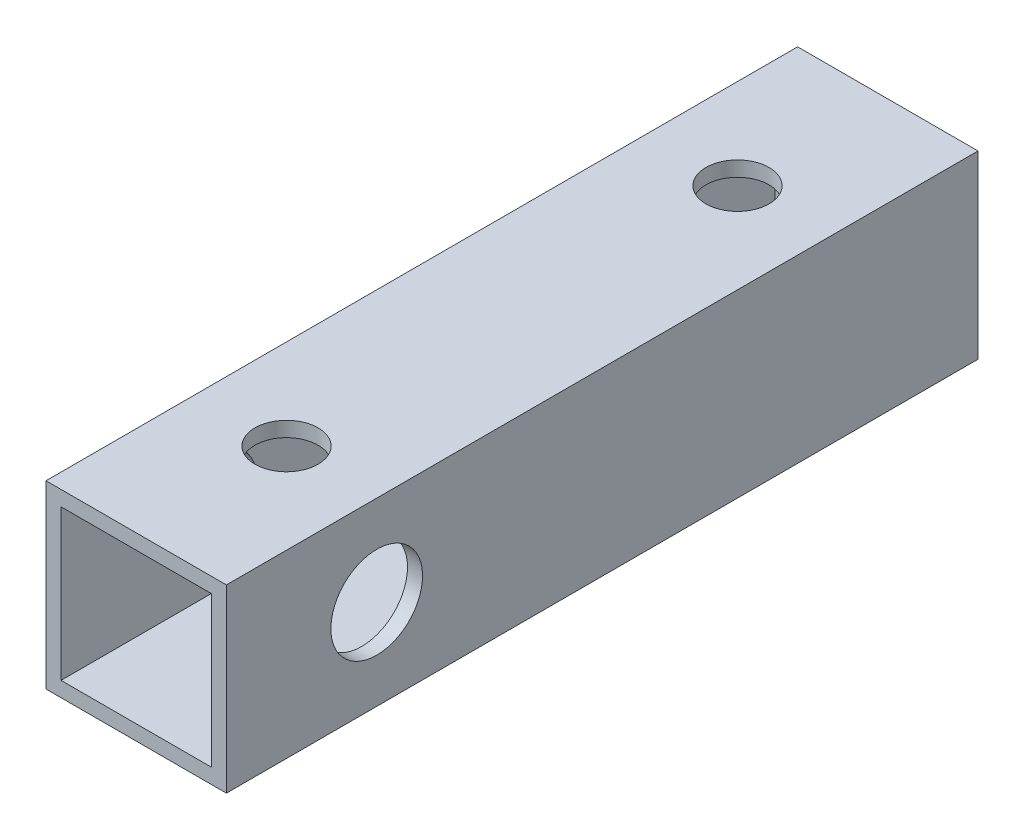
SolidWorks part; units mm, degrees
ref_plane "正面" through (0, 0, 0) normal (0, 0, 1) x (1, 0, 0)
ref_plane "平面" through (0, 0, 0) normal (0, 1, 0) x (1, 0, 0)
ref_plane "右側面" through (0, 0, 0) normal (1, 0, 0) x (0, 0, -1)
sketch "ｽｹｯﾁ1" plane through (0, 0, 0) normal (0, 0, 1) x (1, 0, 0)
  line L1 (-6, 6) -> (6, 6)
  line L2 (-6, 6) -> (-6, -6)
  line L3 (-6, -6) -> (6, -6)
  line L4 (6, 6) -> (6, -6)
  line L5 (-6, 6) -> (6, -6) construction
  line L6 (-6, -6) -> (6, 6) construction
  point P0 (0, 0)
  dimension "D1" = 12
  dimension "D2" = 12
extrude "ﾎﾞｽ - 押し出し1" add sketch "ｽｹｯﾁ1" along normal blind 50
sketch "ｽｹｯﾁ2" plane through (0, 0, 50) normal (0, 0, 1) x (1, 0, 0)
  line L1 (-5, 5) -> (5, 5)
  line L2 (-5, 5) -> (-5, -5)
  line L3 (-5, -5) -> (5, -5)
  line L4 (5, 5) -> (5, -5)
  line L5 (-5, 5) -> (5, -5) construction
  line L6 (-5, -5) -> (5, 5) construction
  point P0 (0, 0)
  dimension "D1" = 10
  dimension "D2" = 10
extrude "ｶｯﾄ - 押し出し1" cut sketch "ｽｹｯﾁ2" against normal blind 47.5
sketch "ｽｹｯﾁ3" plane through (0, 6, 0) normal (0, 1, 0) x (1, 0, 0)
  line L0 (0, 0) -> (0, -10)
  line L1 (0, -50) -> (0, -40)
  line L2 (6, -50) -> (-6, -50) construction
  circle A0 centre (0, -10) radius 2.1
  circle A1 centre (0, -40) radius 2.1
  dimension "D2" = 4.2
  dimension "D4" = 4.2
  dimension "D1" = 10
  dimension "D3" = 10
extrude "ｶｯﾄ - 押し出し2" cut sketch "ｽｹｯﾁ3" against normal blind 47.5
sketch "ｽｹｯﾁ4" plane through (-6, 0, 0) normal (-1, 0, 0) x (0, 0, 1)
  line L0 (0, 0) -> (5, 0)
  circle A0 centre (5, 0) radius 4
  dimension "D2" = 8
  dimension "D1" = 5
sketch "ｽｹｯﾁ5" plane through (-6, 0, 0) normal (-1, 0, 0) x (0, 0, 1)
  line L0 (50, 0) -> (40, 0)
  line L1 (50, 6) -> (50, -6) construction
  circle A0 centre (40, 0) radius 3.05
  dimension "D2" = 6.1
  dimension "D1" = 10
extrude "ｶｯﾄ - 押し出し4" cut sketch "ｽｹｯﾁ5" against normal blind 47.5
